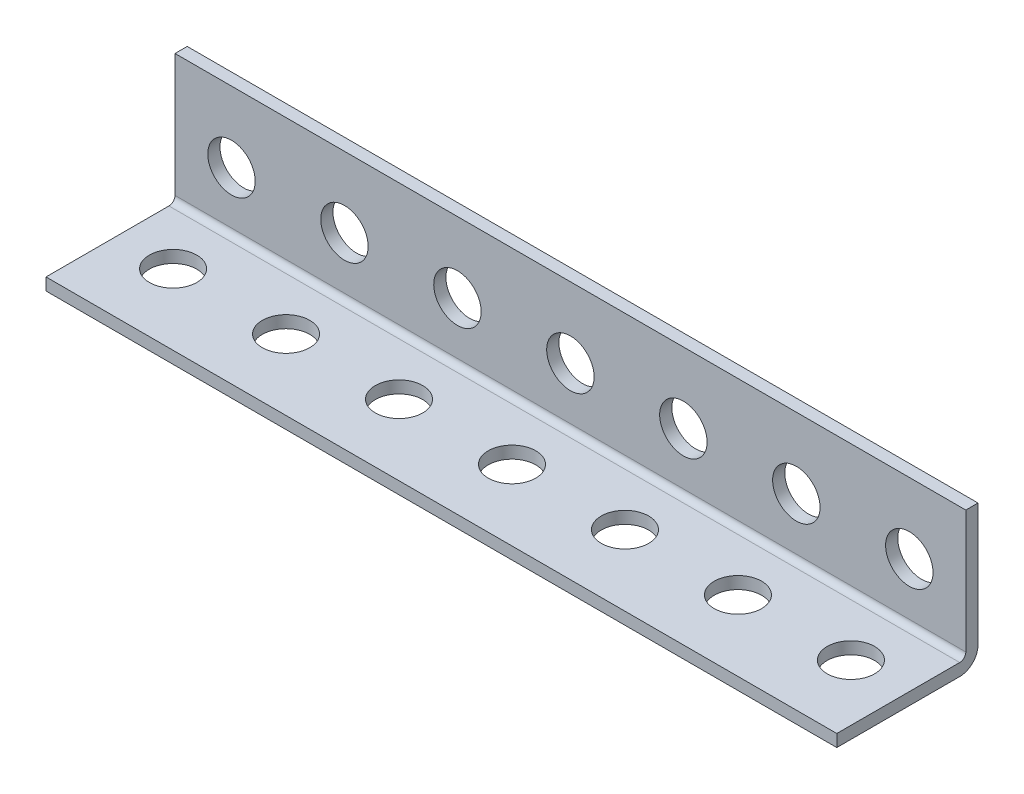
SolidWorks part; units mm, degrees
ref_plane "Front Plane" through (0, 0, 0) normal (0, 0, 1) x (1, 0, 0)
ref_plane "Top Plane" through (0, 0, 0) normal (0, 1, 0) x (1, 0, 0)
ref_plane "Right Plane" through (0, 0, 0) normal (1, 0, 0) x (0, 0, -1)
sketch "Sketch1" plane through (0, 0, 0) normal (1, 0, 0) x (0, 0, -1)
  line L0 (-15.875, -13.1318) -> (13.1318, -13.1318) construction
  line L1 (13.1318, -13.1318) -> (13.1318, 15.875) construction
  line L2 (13.1318, 15.875) -> (15.875, 15.875) construction
  line L3 (15.875, 15.875) -> (15.875, -15.875) construction
  line L4 (15.875, -15.875) -> (-15.875, -15.875) construction
  line L5 (-15.875, -15.875) -> (-15.875, -13.1318) construction
  line L6 (0, -15.875) -> (0, 15.875) construction
  line L7 (15.875, 0) -> (-15.875, 0) construction
  dimension "Thickness | T" = 2.7432
  dimension "Width (A)" = 31.75
  dimension "Width (B)" = 31.75
sketch "Sketch2" plane through (0, 0, 0) normal (0, 0, 1) x (1, 0, 0)
  line L0 (-609.6, 0) -> (609.6, 0) construction
  line L1 (-609.6, 15.875) -> (609.6, 15.875) construction
  line L2 (-609.6, 15.875) -> (-609.6, -15.875) construction
  line L3 (-609.6, -15.875) -> (609.6, -15.875) construction
  line L4 (609.6, 15.875) -> (609.6, -15.875) construction
  line L5 (0, 15.875) -> (0, -15.875) construction
  line L7 (-609.6, -13.1318) -> (609.6, -13.1318) construction
  circle A0 centre (596.9, 0) radius 5.334 construction
  circle A1 centre (571.5, 0) radius 5.334 construction
  point P15 (533.4, 0)
  point P16 (-533.4, 0)
  point P24 (602.234, 0)
  dimension "Mounting Hole Diameter" = 10.668
  dimension "Length | L" = 1219.2
  dimension "Mounting Hole Center to Center" = 25.4
  dimension "D1" = 12.7
  dimension "D2" = 63.5
sketch "Sketch3" plane through (0, 0, 0) normal (0, 1, 0) x (1, 0, 0)
  line L1 (-609.6, 15.875) -> (609.6, 15.875) construction
  line L2 (-609.6, 15.875) -> (-609.6, -15.875) construction
  line L3 (-609.6, -15.875) -> (609.6, -15.875) construction
  line L4 (609.6, 15.875) -> (609.6, -15.875) construction
  line L5 (-609.6, 13.1318) -> (609.6, 13.1318) construction
  line L7 (-609.6, 0) -> (609.6, 0) construction
  circle A0 centre (596.9, 0) radius 5.334 construction
  circle A1 centre (571.5, 0) radius 5.334 construction
  point P19 (-533.4, 0)
  point P21 (602.234, 0)
  point P22 (533.4, 0)
sketch "Sketch4" plane through (0, 0, 0) normal (1, 0, 0) x (0, 0, -1)
  line L0 (-15.875, -13.1318) -> (11.7602, -13.1318)
  line L1 (13.1318, -11.7602) -> (13.1318, 15.875)
  line L2 (13.1318, 15.875) -> (15.875, 15.875)
  line L3 (15.875, 15.875) -> (15.875, -11.7602)
  line L4 (11.7602, -15.875) -> (-15.875, -15.875)
  line L5 (-15.875, -15.875) -> (-15.875, -13.1318)
  line L6 (11.7602, -13.1318) -> (11.7602, -10.3886) construction
  arc A0 (11.7602, -13.1318) -> (13.1318, -11.7602) centre (11.7602, -11.7602) ccw
  arc A1 (15.875, -11.7602) -> (11.7602, -15.875) centre (11.7602, -11.7602) cw
extrude "Boss-Extrude1" add sketch "Sketch4" along normal up to vertex (609.6 mm away) and the other way up to vertex (609.6 mm away) up to point (609.6, 0, 0) other way up to point (-609.6, 0, 0)
sketch "Sketch5" plane through (0, 0, 0) normal (0, 0, 1) x (1, 0, 0)
  circle A0 centre (596.9, 0) radius 5.334
extrude "Cut-Extrude1" cut sketch "Sketch5" against normal through all
sketch "Sketch6" plane through (0, 0, 0) normal (0, 1, 0) x (1, 0, 0)
  circle A0 centre (596.9, 0) radius 5.334
extrude "Cut-Extrude2" cut sketch "Sketch6" against normal through all
pattern_linear "LPattern1" count 48 spacing 25.4 along (-1, 0, 0) of "Cut-Extrude2", "Cut-Extrude1"
sketch "Sketch7" plane through (0, 0, -15.875) normal (0, 0, -1) x (-1, 0, 0)
  line L0 (-609.6, -15.875) -> (609.6, -15.875) construction
  line L1 (-609.6, 15.875) -> (25.4, 15.875)
  line L2 (-609.6, 15.875) -> (-609.6, -15.875)
  line L3 (-609.6, -15.875) -> (25.4, -15.875)
  line L4 (25.4, 15.875) -> (25.4, -15.875)
  line L5 (602.234, 0) -> (609.6, 0) construction
  line L6 (609.6, -11.7602) -> (609.6, 15.875) construction
  line L7 (32.766, 0) -> (25.4, 0)
  circle A0 centre (596.9, 0) radius 5.334 construction
  circle A1 centre (38.1, 0) radius 5.334 construction
  dimension "D1" = 7.366
extrude "Cut-Extrude3" cut sketch "Sketch7" against normal blind 70 contours L4 L1 L2 L3
sketch "Sketch8" plane through (0, 0, -15.875) normal (0, 0, -1) x (-1, 0, 0)
  line L0 (25.4, -15.875) -> (609.6, -15.875) construction
  line L1 (25.4, 15.875) -> (50.8, 15.875)
  line L2 (25.4, 15.875) -> (25.4, -15.875)
  line L3 (25.4, -15.875) -> (50.8, -15.875)
  line L4 (50.8, 15.875) -> (50.8, -15.875)
  line L6 (58.166, 0) -> (50.8, 0)
  circle A0 centre (63.5, 0) radius 5.334 construction
  circle M28 centre (38.1, 0) radius 5.334
  line M29 (25.4, 15.875) -> (25.4, -11.7602)
  line M30 (25.4, -11.7602) -> (609.6, -11.7602)
  line M32 (609.6, 15.875) -> (25.4, 15.875)
  dimension "D1" = 7.366
extrude "Cut-Extrude4" cut sketch "Sketch8" against normal blind 70 contours L4 M32 M29 M30 M28 | L4 L2 L3 M30
sketch "Sketch9" plane through (0, 0, -15.875) normal (0, 0, -1) x (-1, 0, 0)
  line L0 (50.8, -15.875) -> (609.6, -15.875) construction
  line L1 (50.8, 15.875) -> (431.8, 15.875)
  line L2 (50.8, 15.875) -> (50.8, -15.875)
  line L3 (50.8, -15.875) -> (431.8, -15.875)
  line L4 (431.8, 15.875) -> (431.8, -15.875)
  line L5 (439.166, 0) -> (431.8, 0)
  circle A0 centre (444.5, 0) radius 5.334 construction
  circle M7 centre (63.5, 0) radius 5.334
  circle M8 centre (88.9, 0) radius 5.334
  circle M9 centre (114.3, 0) radius 5.334
  circle M10 centre (139.7, 0) radius 5.334
  circle M11 centre (165.1, 0) radius 5.334
  circle M12 centre (190.5, 0) radius 5.334
  circle M13 centre (215.9, 0) radius 5.334
  circle M14 centre (241.3, 0) radius 5.334
  circle M15 centre (266.7, 0) radius 5.334
  circle M16 centre (292.1, 0) radius 5.334
  circle M17 centre (317.5, 0) radius 5.334
  circle M18 centre (342.9, 0) radius 5.334
  circle M19 centre (368.3, 0) radius 5.334
  circle M20 centre (393.7, 0) radius 5.334
  circle M21 centre (419.1, 0) radius 5.334
  line M29 (50.8, 15.875) -> (50.8, -11.7602)
  line M30 (50.8, -11.7602) -> (609.6, -11.7602)
  line M32 (609.6, 15.875) -> (50.8, 15.875)
  dimension "7.366" = 7.366
extrude "Cut-Extrude5" cut sketch "Sketch9" against normal blind 70 contours L4 M32 M29 M30 M8 M10 M12 M14 M16 M18 M20 M21 M19 M17 M15 M13 M11 M9 M7 | L4 L2 L3 M30
equation "\"D1@Sketch2\"= ( \"Length | L@Sketch2\" - \"Mounting Hole Center to Center@Sketch2\" * \"Num Holes\" ) / 2"
equation "\"Num Holes\"= int ( \"Length | L@Sketch2\" / \"Mounting Hole Center to Center@Sketch2\" ) - 1"
equation "\"D2@Sketch2\"=\"Mounting Hole Center to Center@Sketch2\"*2.5"
equation "\"D3@LPattern1\"=\"Mounting Hole Center to Center@Sketch2\""
